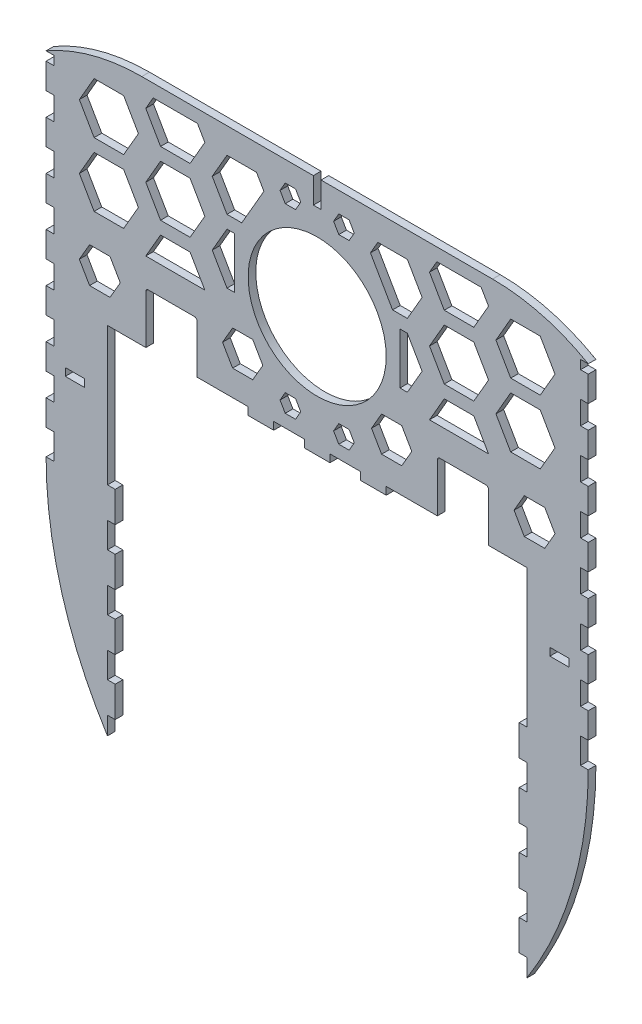
SolidWorks part; units mm, degrees
material "birch 3mm plywood"
ref_plane "Front" through (0, 0, 0) normal (0, 0, 1) x (1, 0, 0)
ref_plane "Top" through (0, 0, 0) normal (0, 1, 0) x (1, 0, 0)
ref_plane "Right" through (0, 0, 0) normal (1, 0, 0) x (0, 0, -1)
sketch "Sketch1" plane through (0, 0, 0) normal (0, 0, 1) x (1, 0, 0)
  line L0 (-106, 24.7134) -> (-106, 14.7134) construction
  line L1 (-82, 17.2134) -> (-82, 27.2134)
  line L2 (-103, 152.2134) -> (-106, 152.2134) construction
  line L3 (-103, 14.7134) -> (-106, 14.7134) construction
  line L4 (-103, 152.2134) -> (-103, 14.7134) construction
  line L5 (-47, 71.2134) -> (-27, 71.2134)
  line L7 (-103, 152.2134) -> (-106, 152.2134)
  line L8 (-103, 14.7134) -> (-106, 14.7134)
  line L9 (-103, 152.2134) -> (-103, 148.7134)
  line L10 (0, 0) -> (0, 68.2134) construction
  line L11 (-82, -67.7866) -> (-82, -60.7866)
  line L12 (-68.5834, 162.2134) -> (68.5834, 162.2134)
  line L13 (-82, 27.2134) -> (-82, 71.2134)
  line L18 (-47, 71.2134) -> (-47, 90.2134)
  line L19 (-48, 91.2134) -> (-66, 91.2134)
  line L20 (-67, 90.2134) -> (-67, 71.2134)
  line L22 (-103, 24.7134) -> (-106, 24.7134)
  line L24 (-103, 34.7134) -> (-106, 34.7134)
  line L25 (-106, 24.7134) -> (-106, 34.7134)
  line L26 (-103, 43.7134) -> (-106, 43.7134)
  line L27 (-106, 43.7134) -> (-106, 53.7134)
  line L28 (-103, 53.7134) -> (-106, 53.7134)
  line L30 (-103, 62.7134) -> (-106, 62.7134)
  line L31 (-106, 62.7134) -> (-106, 72.7134)
  line L32 (-103, 72.7134) -> (-106, 72.7134)
  line L34 (-103, 81.7134) -> (-106, 81.7134)
  line L35 (-106, 81.7134) -> (-106, 91.7134)
  line L36 (-103, 91.7134) -> (-106, 91.7134)
  line L38 (-103, 100.7134) -> (-106, 100.7134)
  line L39 (-106, 100.7134) -> (-106, 110.7134)
  line L40 (-103, 110.7134) -> (-106, 110.7134)
  line L42 (-103, 119.7134) -> (-106, 119.7134)
  line L43 (-106, 119.7134) -> (-106, 129.7134)
  line L44 (-103, 129.7134) -> (-106, 129.7134)
  line L46 (-103, 138.7134) -> (-106, 138.7134)
  line L47 (-106, 138.7134) -> (-106, 148.7134)
  line L48 (-103, 148.7134) -> (-106, 148.7134)
  line L49 (-103, 138.7134) -> (-103, 129.7134)
  line L50 (-103, 119.7134) -> (-103, 110.7134)
  line L51 (-103, 100.7134) -> (-103, 91.7134)
  line L52 (-103, 81.7134) -> (-103, 72.7134)
  line L53 (-103, 62.7134) -> (-103, 53.7134)
  line L54 (-103, 43.7134) -> (-103, 34.7134)
  line L55 (-103, 24.7134) -> (-103, 14.7134)
  line L56 (-82, 71.2134) -> (-67, 71.2134)
  line L57 (-82, 17.2134) -> (-82, 27.2134)
  line L58 (-82, -4.7866) -> (-82, 5.2134)
  line L59 (-82, -26.7866) -> (-82, -16.7866)
  line L60 (-17, 71.2134) -> (-5, 71.2134)
  line L61 (-82, -48.7866) -> (-82, -38.7866)
  line L62 (106, 24.7134) -> (106, 14.7134) construction
  line L63 (79, -16.7866) -> (82, -16.7866)
  line L64 (79, -4.7866) -> (79, -16.7866)
  line L65 (82, -4.7866) -> (79, -4.7866)
  line L66 (82, 5.2134) -> (82, -4.7866)
  line L67 (79, 5.2134) -> (82, 5.2134)
  line L68 (79, 17.2134) -> (79, 5.2134)
  line L69 (82, 17.2134) -> (79, 17.2134)
  line L70 (82, 27.2134) -> (82, 17.2134)
  line L71 (0, 162.2134) -> (0, 68.2134) construction
  line L78 (82, 71.2134) -> (82, 27.2134)
  line L79 (67, 71.2134) -> (82, 71.2134)
  line L80 (-88.6, 48.7134) -> (-93.6, 48.7134)
  line L81 (-82, -16.7866) -> (-82, -26.7866)
  line L82 (-98.6, 45.7134) -> (-98.6, 45.0905)
  line L83 (-82, -26.7866) -> (-79, -26.7866)
  line L84 (-82, 45.7134) -> (-88.6, 45.7134)
  line L85 (-79, -26.7866) -> (-79, -38.7866)
  line L86 (-88.6, 45.7134) -> (-88.6, 48.7134)
  line L87 (-79, -38.7866) -> (-82, -38.7866)
  line L89 (-82, -67.7866) -> (82, -67.7866)
  line L110 (82, 45.7134) -> (82, 49.2134)
  line L111 (82, 49.2134) -> (79, 49.2134)
  line L112 (79, 49.2134) -> (79, 61.2134)
  line L113 (79, 61.2134) -> (82, 61.2134)
  line L114 (82, 61.2134) -> (82, 71.2134)
  line L115 (82, 71.2134) -> (71, 71.2134)
  line L116 (71, 71.2134) -> (71, 68.2134)
  line L117 (71, 68.2134) -> (61, 68.2134)
  line L118 (61, 68.2134) -> (61, 71.2134)
  line L119 (61, 71.2134) -> (49, 71.2134)
  line L120 (49, 71.2134) -> (49, 68.2134)
  line L121 (49, 68.2134) -> (39, 68.2134)
  line L122 (39, 68.2134) -> (39, 71.2134)
  line L123 (39, 71.2134) -> (27, 71.2134)
  line L124 (27, 71.2134) -> (27, 68.2134)
  line L125 (27, 68.2134) -> (17, 68.2134)
  line L126 (17, 68.2134) -> (17, 71.2134)
  line L127 (17, 71.2134) -> (5, 71.2134)
  line L128 (5, 71.2134) -> (5, 68.2134)
  line L129 (5, 68.2134) -> (-5, 68.2134)
  line L130 (-5, 68.2134) -> (-5, 71.2134)
  line L131 (-5, 71.2134) -> (-17, 71.2134)
  line L132 (-17, 71.2134) -> (-17, 68.2134)
  line L133 (-17, 68.2134) -> (-27, 68.2134)
  line L134 (-27, 68.2134) -> (-27, 71.2134)
  line L135 (-27, 71.2134) -> (-39, 71.2134)
  line L136 (-39, 71.2134) -> (-39, 68.2134)
  line L137 (-39, 68.2134) -> (-49, 68.2134)
  line L138 (-49, 68.2134) -> (-49, 71.2134)
  line L139 (-49, 71.2134) -> (-61, 71.2134)
  line L140 (-61, 71.2134) -> (-61, 68.2134)
  line L141 (-61, 68.2134) -> (-71, 68.2134)
  line L142 (-71, 68.2134) -> (-71, 71.2134)
  line L143 (-71, 71.2134) -> (-82, 71.2134)
  line L144 (-82, 71.2134) -> (-82, 61.2134)
  line L145 (-82, 61.2134) -> (-79, 61.2134)
  line L146 (-79, 61.2134) -> (-79, 49.2134)
  line L147 (-79, 49.2134) -> (-82, 49.2134)
  line L148 (-82, 49.2134) -> (-82, 45.7134)
  line L209 (5, 68.2134) -> (-5, 68.2134)
  line L210 (-5, 68.2134) -> (-5, 71.2134)
  line L211 (-5, 71.2134) -> (-17, 71.2134)
  line L212 (-17, 71.2134) -> (-17, 68.2134)
  line L213 (-17, 68.2134) -> (-27, 68.2134)
  line L214 (-27, 68.2134) -> (-27, 71.2134)
  line L215 (-27, 71.2134) -> (-47, 71.2134)
  line L223 (-67, 71.2134) -> (-82, 71.2134)
  line L240 (27, 71.2134) -> (47, 71.2134)
  line L241 (27, 68.2134) -> (27, 71.2134)
  line L242 (17, 68.2134) -> (27, 68.2134)
  line L243 (17, 71.2134) -> (17, 68.2134)
  line L244 (5, 71.2134) -> (17, 71.2134)
  line L245 (5, 68.2134) -> (5, 71.2134)
  line L246 (82, -60.7866) -> (82, -67.7866)
  line L247 (79, -60.7866) -> (82, -60.7866)
  line L248 (79, -48.7866) -> (79, -60.7866)
  line L249 (82, -48.7866) -> (79, -48.7866)
  line L250 (82, -38.7866) -> (82, -48.7866)
  line L251 (79, -38.7866) -> (82, -38.7866)
  line L252 (79, -26.7866) -> (79, -38.7866)
  line L253 (82, -26.7866) -> (79, -26.7866)
  line L254 (82, -16.7866) -> (82, -26.7866)
  line L255 (82, -48.7866) -> (82, -38.7866)
  line L256 (17, 71.2134) -> (5, 71.2134)
  line L257 (82, -26.7866) -> (82, -16.7866)
  line L258 (82, -4.7866) -> (82, 5.2134)
  line L259 (82, 17.2134) -> (82, 27.2134)
  line L260 (82, 71.2134) -> (67, 71.2134)
  line L261 (103, 24.7134) -> (103, 14.7134)
  line L262 (103, 43.7134) -> (103, 34.7134)
  line L263 (103, 62.7134) -> (103, 53.7134)
  line L264 (103, 81.7134) -> (103, 72.7134)
  line L265 (103, 100.7134) -> (103, 91.7134)
  line L266 (103, 119.7134) -> (103, 110.7134)
  line L267 (103, 138.7134) -> (103, 129.7134)
  line L268 (103, 148.7134) -> (106, 148.7134)
  line L269 (106, 138.7134) -> (106, 148.7134)
  line L270 (103, 138.7134) -> (106, 138.7134)
  line L271 (103, 129.7134) -> (106, 129.7134)
  line L272 (106, 119.7134) -> (106, 129.7134)
  line L273 (103, 119.7134) -> (106, 119.7134)
  line L274 (103, 110.7134) -> (106, 110.7134)
  line L275 (106, 100.7134) -> (106, 110.7134)
  line L276 (103, 100.7134) -> (106, 100.7134)
  line L277 (103, 91.7134) -> (106, 91.7134)
  line L278 (106, 81.7134) -> (106, 91.7134)
  line L279 (103, 81.7134) -> (106, 81.7134)
  line L280 (103, 72.7134) -> (106, 72.7134)
  line L281 (106, 62.7134) -> (106, 72.7134)
  line L282 (103, 62.7134) -> (106, 62.7134)
  line L283 (103, 53.7134) -> (106, 53.7134)
  line L284 (106, 43.7134) -> (106, 53.7134)
  line L285 (103, 43.7134) -> (106, 43.7134)
  line L286 (106, 24.7134) -> (106, 34.7134)
  line L287 (103, 34.7134) -> (106, 34.7134)
  line L288 (103, 24.7134) -> (106, 24.7134)
  line L289 (67, 90.2134) -> (67, 71.2134)
  line L290 (48, 91.2134) -> (66, 91.2134)
  line L291 (47, 71.2134) -> (47, 90.2134)
  line L293 (82, -67.7866) -> (82, -60.7866)
  line L294 (103, 152.2134) -> (103, 148.7134)
  line L295 (103, 14.7134) -> (106, 14.7134)
  line L296 (103, 152.2134) -> (106, 152.2134)
  line L297 (-82, -38.7866) -> (-82, -48.7866)
  line L298 (47, 71.2134) -> (27, 71.2134)
  line L299 (0, 162.2134) -> (0, 189.65) construction
  line L300 (-82, -48.7866) -> (-79, -48.7866)
  line L301 (82, 17.2134) -> (82, 27.2134)
  line L404 (-79, -48.7866) -> (-79, -60.7866)
  line L405 (-79, -60.7866) -> (-82, -60.7866)
  line L406 (-82, -60.7866) -> (-82, -67.7866)
  line L407 (-82, 71.2134) -> (-82, 27.2134)
  line L408 (-82, 27.2134) -> (-82, 17.2134)
  line L409 (-82, 17.2134) -> (-79, 17.2134)
  line L410 (-79, 17.2134) -> (-79, 5.2134)
  line L411 (-79, 5.2134) -> (-82, 5.2134)
  line L412 (-82, 5.2134) -> (-82, -4.7866)
  line L413 (-82, -4.7866) -> (-79, -4.7866)
  line L414 (-79, -4.7866) -> (-79, -16.7866)
  line L415 (-79, -16.7866) -> (-82, -16.7866)
  line L456 (-93.6, 48.7134) -> (-93.6, 45.7134)
  line L458 (-93.6, 45.7134) -> (-98.6, 45.7134)
  line L460 (98.6, 45.0905) -> (98.6, 45.7134)
  line L462 (98.6, 45.7134) -> (93.6, 45.7134)
  line L464 (93.6, 45.7134) -> (93.6, 48.7134)
  line L466 (93.6, 48.7134) -> (88.6, 48.7134)
  line L468 (88.6, 48.7134) -> (88.6, 45.7134)
  line L470 (88.6, 45.7134) -> (82, 45.7134)
  arc A0 (-68.5834, 162.2134) -> (-106, 152.2134) centre (-68.5834, 87.2134) ccw
  arc A1 (-106, 14.7134) -> (-82, -67.7866) centre (47.7969, 14.7134) ccw
  arc A4 (-47, 90.2134) -> (-48, 91.2134) centre (-48, 90.2134) ccw
  arc A5 (-66, 91.2134) -> (-67, 90.2134) centre (-66, 90.2134) ccw
  arc A6 (66, 91.2134) -> (67, 90.2134) centre (66, 90.2134) cw
  arc A7 (47, 90.2134) -> (48, 91.2134) centre (48, 90.2134) cw
  arc A8 (106, 14.7134) -> (82, -67.7866) centre (-47.7969, 14.7134) cw
  arc A9 (68.5834, 162.2134) -> (106, 152.2134) centre (68.5834, 87.2134) cw
  circle A10 centre (0, 115.2134) radius 27
  arc A15 (-98.6, 45.0905) -> (-82, -67.7866) centre (293.4723, 45.0905) ccw
  arc A17 (82, -67.7866) -> (98.6, 45.0905) centre (-293.4723, 45.0905) ccw
  dimension "D8" = 75
  dimension "D9" = 20
  dimension "D10" = 15
  dimension "D12" = 1
  dimension "D13" = 1
  dimension "D2" = 10
  dimension "D3" = 20
  dimension "D4" = 10
  dimension "D5" = 10
  dimension "D7" = 9
  dimension "D11" = 20
  dimension "D14" = 3
  dimension "D15" = 3
  dimension "D16" = 12
  dimension "D17" = 10
  dimension "D1" = 0
  dimension "D6" = 7
extrude "Boss-Extrude1" add sketch "Sketch1" along normal blind 3
sketch "Sketch2" plane through (0, 0, 3) normal (0, 0, 1) x (1, 0, 0)
  line L4 (-98.5, 45.7134) -> (-91, 45.7134)
  line L5 (-91, 45.7134) -> (-91, 48.7134)
  line L6 (-91, 48.7134) -> (-98.5, 48.7134)
  line L7 (-98.5, 48.7134) -> (-98.5, 45.7134)
  line L8 (-98.5, 45.7134) -> (-91, 45.7134)
  line L9 (-91, 45.7134) -> (-91, 48.7134)
  line L10 (-91, 48.7134) -> (-98.5, 48.7134)
  line L11 (-98.5, 48.7134) -> (-98.5, 45.7134)
  line L12 (91, 45.7134) -> (98.5, 45.7134)
  line L13 (98.5, 45.7134) -> (98.5, 48.7134)
  line L14 (98.5, 48.7134) -> (91, 48.7134)
  line L15 (91, 48.7134) -> (91, 45.7134)
  line L16 (91, 45.7134) -> (98.5, 45.7134)
  line L17 (98.5, 45.7134) -> (98.5, 48.7134)
  line L18 (98.5, 48.7134) -> (91, 48.7134)
  line L19 (91, 48.7134) -> (91, 45.7134)
  line L20 (-1.5, 162.2134) -> (-1.5, 152.2134)
  line L21 (-1.5, 152.2134) -> (1.5, 152.2134)
  line L22 (1.5, 152.2134) -> (1.5, 162.2134)
  line L23 (1.5, 162.2134) -> (-1.5, 162.2134)
  line L24 (-1.5, 162.2134) -> (-1.5, 152.2134)
  line L25 (-1.5, 152.2134) -> (1.5, 152.2134)
  line L26 (1.5, 152.2134) -> (1.5, 162.2134)
  line L27 (1.5, 162.2134) -> (-1.5, 162.2134)
  line L118 (68.5834, 162.2134) -> (-68.5834, 162.2134)
  line L119 (-106, 152.2134) -> (-103, 152.2134)
  line L120 (-103, 152.2134) -> (-103, 148.7134)
  line L121 (-103, 148.7134) -> (-106, 148.7134)
  line L122 (-106, 148.7134) -> (-106, 138.7134)
  line L123 (-106, 138.7134) -> (-103, 138.7134)
  line L124 (-103, 138.7134) -> (-103, 129.7134)
  line L125 (-103, 129.7134) -> (-106, 129.7134)
  line L126 (-106, 129.7134) -> (-106, 119.7134)
  line L127 (-106, 119.7134) -> (-103, 119.7134)
  line L128 (-103, 119.7134) -> (-103, 110.7134)
  line L129 (-103, 110.7134) -> (-106, 110.7134)
  line L130 (-106, 110.7134) -> (-106, 100.7134)
  line L131 (-106, 100.7134) -> (-103, 100.7134)
  line L132 (-103, 100.7134) -> (-103, 91.7134)
  line L133 (-103, 91.7134) -> (-106, 91.7134)
  line L134 (-106, 91.7134) -> (-106, 81.7134)
  line L135 (-106, 81.7134) -> (-103, 81.7134)
  line L136 (-103, 81.7134) -> (-103, 72.7134)
  line L137 (-103, 72.7134) -> (-106, 72.7134)
  line L138 (-106, 72.7134) -> (-106, 62.7134)
  line L139 (-106, 62.7134) -> (-103, 62.7134)
  line L140 (-103, 62.7134) -> (-103, 53.7134)
  line L141 (-103, 53.7134) -> (-106, 53.7134)
  line L142 (-106, 53.7134) -> (-106, 43.7134)
  line L143 (-106, 43.7134) -> (-103, 43.7134)
  line L144 (-103, 43.7134) -> (-103, 34.7134)
  line L145 (-103, 34.7134) -> (-106, 34.7134)
  line L146 (-106, 34.7134) -> (-106, 24.7134)
  line L147 (-106, 24.7134) -> (-103, 24.7134)
  line L148 (-103, 24.7134) -> (-103, 14.7134)
  line L149 (-103, 14.7134) -> (-106, 14.7134)
  line L150 (-82, -67.7866) -> (-82, -60.7866)
  line L151 (-82, -60.7866) -> (-79, -60.7866)
  line L152 (-79, -60.7866) -> (-79, -48.7866)
  line L153 (-79, -48.7866) -> (-82, -48.7866)
  line L154 (-82, -48.7866) -> (-82, -38.7866)
  line L155 (-82, -38.7866) -> (-79, -38.7866)
  line L156 (-79, -38.7866) -> (-79, -26.7866)
  line L157 (-79, -26.7866) -> (-82, -26.7866)
  line L158 (-82, -26.7866) -> (-82, -16.7866)
  line L159 (-82, -16.7866) -> (-79, -16.7866)
  line L160 (-79, -16.7866) -> (-79, -4.7866)
  line L161 (-79, -4.7866) -> (-82, -4.7866)
  line L162 (-82, -4.7866) -> (-82, 5.2134)
  line L163 (-82, 5.2134) -> (-79, 5.2134)
  line L164 (-79, 5.2134) -> (-79, 17.2134)
  line L165 (-79, 17.2134) -> (-82, 17.2134)
  line L166 (-82, 17.2134) -> (-82, 71.2134)
  line L167 (-82, 71.2134) -> (-67, 71.2134)
  line L168 (-67, 71.2134) -> (-67, 90.2134)
  line L169 (-66, 91.2134) -> (-48, 91.2134)
  line L170 (-47, 90.2134) -> (-47, 71.2134)
  line L171 (-47, 71.2134) -> (-27, 71.2134)
  line L172 (-27, 71.2134) -> (-27, 68.2134)
  line L173 (-27, 68.2134) -> (-17, 68.2134)
  line L174 (-17, 68.2134) -> (-17, 71.2134)
  line L175 (-17, 71.2134) -> (-5, 71.2134)
  line L176 (-5, 71.2134) -> (-5, 68.2134)
  line L177 (-5, 68.2134) -> (5, 68.2134)
  line L178 (5, 68.2134) -> (5, 71.2134)
  line L179 (5, 71.2134) -> (17, 71.2134)
  line L180 (17, 71.2134) -> (17, 68.2134)
  line L181 (17, 68.2134) -> (27, 68.2134)
  line L182 (27, 68.2134) -> (27, 71.2134)
  line L183 (27, 71.2134) -> (47, 71.2134)
  line L184 (47, 71.2134) -> (47, 90.2134)
  line L185 (48, 91.2134) -> (66, 91.2134)
  line L186 (67, 90.2134) -> (67, 71.2134)
  line L187 (67, 71.2134) -> (82, 71.2134)
  line L188 (82, 71.2134) -> (82, 17.2134)
  line L189 (82, 17.2134) -> (79, 17.2134)
  line L190 (79, 17.2134) -> (79, 5.2134)
  line L191 (79, 5.2134) -> (82, 5.2134)
  line L192 (82, 5.2134) -> (82, -4.7866)
  line L193 (82, -4.7866) -> (79, -4.7866)
  line L194 (79, -4.7866) -> (79, -16.7866)
  line L195 (79, -16.7866) -> (82, -16.7866)
  line L196 (82, -16.7866) -> (82, -26.7866)
  line L197 (82, -26.7866) -> (79, -26.7866)
  line L198 (79, -26.7866) -> (79, -38.7866)
  line L199 (79, -38.7866) -> (82, -38.7866)
  line L200 (82, -38.7866) -> (82, -48.7866)
  line L201 (82, -48.7866) -> (79, -48.7866)
  line L202 (79, -48.7866) -> (79, -60.7866)
  line L203 (79, -60.7866) -> (82, -60.7866)
  line L204 (82, -60.7866) -> (82, -67.7866)
  line L205 (106, 14.7134) -> (103, 14.7134)
  line L206 (103, 14.7134) -> (103, 24.7134)
  line L207 (103, 24.7134) -> (106, 24.7134)
  line L208 (106, 24.7134) -> (106, 34.7134)
  line L209 (106, 34.7134) -> (103, 34.7134)
  line L210 (103, 34.7134) -> (103, 43.7134)
  line L211 (103, 43.7134) -> (106, 43.7134)
  line L212 (106, 43.7134) -> (106, 53.7134)
  line L213 (106, 53.7134) -> (103, 53.7134)
  line L214 (103, 53.7134) -> (103, 62.7134)
  line L215 (103, 62.7134) -> (106, 62.7134)
  line L216 (106, 62.7134) -> (106, 72.7134)
  line L217 (106, 72.7134) -> (103, 72.7134)
  line L218 (103, 72.7134) -> (103, 81.7134)
  line L219 (103, 81.7134) -> (106, 81.7134)
  line L220 (106, 81.7134) -> (106, 91.7134)
  line L221 (106, 91.7134) -> (103, 91.7134)
  line L222 (103, 91.7134) -> (103, 100.7134)
  line L223 (103, 100.7134) -> (106, 100.7134)
  line L224 (106, 100.7134) -> (106, 110.7134)
  line L225 (106, 110.7134) -> (103, 110.7134)
  line L226 (103, 110.7134) -> (103, 119.7134)
  line L227 (103, 119.7134) -> (106, 119.7134)
  line L228 (106, 119.7134) -> (106, 129.7134)
  line L229 (106, 129.7134) -> (103, 129.7134)
  line L230 (103, 129.7134) -> (103, 138.7134)
  line L231 (103, 138.7134) -> (106, 138.7134)
  line L232 (106, 138.7134) -> (106, 148.7134)
  line L233 (106, 148.7134) -> (103, 148.7134)
  line L234 (103, 148.7134) -> (103, 152.2134)
  line L235 (103, 152.2134) -> (106, 152.2134)
  line L236 (68.5834, 162.2134) -> (-68.5834, 162.2134)
  line L237 (-106, 152.2134) -> (-103, 152.2134)
  line L238 (-103, 152.2134) -> (-103, 148.7134)
  line L239 (-103, 148.7134) -> (-106, 148.7134)
  line L240 (-106, 148.7134) -> (-106, 138.7134)
  line L241 (-106, 138.7134) -> (-103, 138.7134)
  line L242 (-103, 138.7134) -> (-103, 129.7134)
  line L243 (-103, 129.7134) -> (-106, 129.7134)
  line L244 (-106, 129.7134) -> (-106, 119.7134)
  line L245 (-106, 119.7134) -> (-103, 119.7134)
  line L246 (-103, 119.7134) -> (-103, 110.7134)
  line L247 (-103, 110.7134) -> (-106, 110.7134)
  line L248 (-106, 110.7134) -> (-106, 100.7134)
  line L249 (-106, 100.7134) -> (-103, 100.7134)
  line L250 (-103, 100.7134) -> (-103, 91.7134)
  line L251 (-103, 91.7134) -> (-106, 91.7134)
  line L252 (-106, 91.7134) -> (-106, 81.7134)
  line L253 (-106, 81.7134) -> (-103, 81.7134)
  line L254 (-103, 81.7134) -> (-103, 72.7134)
  line L255 (-103, 72.7134) -> (-106, 72.7134)
  line L256 (-106, 72.7134) -> (-106, 62.7134)
  line L257 (-106, 62.7134) -> (-103, 62.7134)
  line L258 (-103, 62.7134) -> (-103, 53.7134)
  line L259 (-103, 53.7134) -> (-106, 53.7134)
  line L260 (-106, 53.7134) -> (-106, 43.7134)
  line L261 (-106, 43.7134) -> (-103, 43.7134)
  line L262 (-103, 43.7134) -> (-103, 34.7134)
  line L263 (-103, 34.7134) -> (-106, 34.7134)
  line L264 (-106, 34.7134) -> (-106, 24.7134)
  line L265 (-106, 24.7134) -> (-103, 24.7134)
  line L266 (-103, 24.7134) -> (-103, 14.7134)
  line L267 (-103, 14.7134) -> (-106, 14.7134)
  line L268 (-82, -67.7866) -> (-82, -60.7866)
  line L269 (-82, -60.7866) -> (-79, -60.7866)
  line L270 (-79, -60.7866) -> (-79, -48.7866)
  line L271 (-79, -48.7866) -> (-82, -48.7866)
  line L272 (-82, -48.7866) -> (-82, -38.7866)
  line L273 (-82, -38.7866) -> (-79, -38.7866)
  line L274 (-79, -38.7866) -> (-79, -26.7866)
  line L275 (-79, -26.7866) -> (-82, -26.7866)
  line L276 (-82, -26.7866) -> (-82, -16.7866)
  line L277 (-82, -16.7866) -> (-79, -16.7866)
  line L278 (-79, -16.7866) -> (-79, -4.7866)
  line L279 (-79, -4.7866) -> (-82, -4.7866)
  line L280 (-82, -4.7866) -> (-82, 5.2134)
  line L281 (-82, 5.2134) -> (-79, 5.2134)
  line L282 (-79, 5.2134) -> (-79, 17.2134)
  line L283 (-79, 17.2134) -> (-82, 17.2134)
  line L284 (-82, 17.2134) -> (-82, 71.2134)
  line L285 (-82, 71.2134) -> (-67, 71.2134)
  line L286 (-67, 71.2134) -> (-67, 90.2134)
  line L287 (-66, 91.2134) -> (-48, 91.2134)
  line L288 (-47, 90.2134) -> (-47, 71.2134)
  line L289 (-47, 71.2134) -> (-27, 71.2134)
  line L290 (-27, 71.2134) -> (-27, 68.2134)
  line L291 (-27, 68.2134) -> (-17, 68.2134)
  line L292 (-17, 68.2134) -> (-17, 71.2134)
  line L293 (-17, 71.2134) -> (-5, 71.2134)
  line L294 (-5, 71.2134) -> (-5, 68.2134)
  line L295 (-5, 68.2134) -> (5, 68.2134)
  line L296 (5, 68.2134) -> (5, 71.2134)
  line L297 (5, 71.2134) -> (17, 71.2134)
  line L298 (17, 71.2134) -> (17, 68.2134)
  line L299 (17, 68.2134) -> (27, 68.2134)
  line L300 (27, 68.2134) -> (27, 71.2134)
  line L301 (27, 71.2134) -> (47, 71.2134)
  line L302 (47, 71.2134) -> (47, 90.2134)
  line L303 (48, 91.2134) -> (66, 91.2134)
  line L304 (67, 90.2134) -> (67, 71.2134)
  line L305 (67, 71.2134) -> (82, 71.2134)
  line L306 (82, 71.2134) -> (82, 17.2134)
  line L307 (82, 17.2134) -> (79, 17.2134)
  line L308 (79, 17.2134) -> (79, 5.2134)
  line L309 (79, 5.2134) -> (82, 5.2134)
  line L310 (82, 5.2134) -> (82, -4.7866)
  line L311 (82, -4.7866) -> (79, -4.7866)
  line L312 (79, -4.7866) -> (79, -16.7866)
  line L313 (79, -16.7866) -> (82, -16.7866)
  line L314 (82, -16.7866) -> (82, -26.7866)
  line L315 (82, -26.7866) -> (79, -26.7866)
  line L316 (79, -26.7866) -> (79, -38.7866)
  line L317 (79, -38.7866) -> (82, -38.7866)
  line L318 (82, -38.7866) -> (82, -48.7866)
  line L319 (82, -48.7866) -> (79, -48.7866)
  line L320 (79, -48.7866) -> (79, -60.7866)
  line L321 (79, -60.7866) -> (82, -60.7866)
  line L322 (82, -60.7866) -> (82, -67.7866)
  line L323 (106, 14.7134) -> (103, 14.7134)
  line L324 (103, 14.7134) -> (103, 24.7134)
  line L325 (103, 24.7134) -> (106, 24.7134)
  line L326 (106, 24.7134) -> (106, 34.7134)
  line L327 (106, 34.7134) -> (103, 34.7134)
  line L328 (103, 34.7134) -> (103, 43.7134)
  line L329 (103, 43.7134) -> (106, 43.7134)
  line L330 (106, 43.7134) -> (106, 53.7134)
  line L331 (106, 53.7134) -> (103, 53.7134)
  line L332 (103, 53.7134) -> (103, 62.7134)
  line L333 (103, 62.7134) -> (106, 62.7134)
  line L334 (106, 62.7134) -> (106, 72.7134)
  line L335 (106, 72.7134) -> (103, 72.7134)
  line L336 (103, 72.7134) -> (103, 81.7134)
  line L337 (103, 81.7134) -> (106, 81.7134)
  line L338 (106, 81.7134) -> (106, 91.7134)
  line L339 (106, 91.7134) -> (103, 91.7134)
  line L340 (103, 91.7134) -> (103, 100.7134)
  line L341 (103, 100.7134) -> (106, 100.7134)
  line L342 (106, 100.7134) -> (106, 110.7134)
  line L343 (106, 110.7134) -> (103, 110.7134)
  line L344 (103, 110.7134) -> (103, 119.7134)
  line L345 (103, 119.7134) -> (106, 119.7134)
  line L346 (106, 119.7134) -> (106, 129.7134)
  line L347 (106, 129.7134) -> (103, 129.7134)
  line L348 (103, 129.7134) -> (103, 138.7134)
  line L349 (103, 138.7134) -> (106, 138.7134)
  line L350 (106, 138.7134) -> (106, 148.7134)
  line L351 (106, 148.7134) -> (103, 148.7134)
  line L352 (103, 148.7134) -> (103, 152.2134)
  line L353 (103, 152.2134) -> (106, 152.2134)
  arc A8 (106, 152.2134) -> (68.5834, 162.2134) centre (68.5834, 87.2134) ccw
  arc A9 (-68.5834, 162.2134) -> (-106, 152.2134) centre (-68.5834, 87.2134) ccw
  arc A10 (-106, 14.7134) -> (-82, -67.7866) centre (47.7969, 14.7134) ccw
  arc A11 (-66, 91.2134) -> (-67, 90.2134) centre (-66, 90.2134) ccw
  arc A12 (-47, 90.2134) -> (-48, 91.2134) centre (-48, 90.2134) ccw
  arc A13 (48, 91.2134) -> (47, 90.2134) centre (48, 90.2134) ccw
  arc A14 (67, 90.2134) -> (66, 91.2134) centre (66, 90.2134) ccw
  arc A15 (82, -67.7866) -> (106, 14.7134) centre (-47.7969, 14.7134) ccw
  arc A16 (106, 152.2134) -> (68.5834, 162.2134) centre (68.5834, 87.2134) ccw
  arc A17 (-68.5834, 162.2134) -> (-106, 152.2134) centre (-68.5834, 87.2134) ccw
  arc A18 (-106, 14.7134) -> (-82, -67.7866) centre (47.7969, 14.7134) ccw
  arc A19 (-66, 91.2134) -> (-67, 90.2134) centre (-66, 90.2134) ccw
  arc A20 (-47, 90.2134) -> (-48, 91.2134) centre (-48, 90.2134) ccw
  arc A21 (48, 91.2134) -> (47, 90.2134) centre (48, 90.2134) ccw
  arc A22 (67, 90.2134) -> (66, 91.2134) centre (66, 90.2134) ccw
  arc A23 (82, -67.7866) -> (106, 14.7134) centre (-47.7969, 14.7134) ccw
  dimension "D1" = 0
  dimension "D2" = 0
  dimension "D3" = 0
  dimension "D4" = 0
extrude "Cut-Extrude1" cut sketch "Sketch2" against normal blind 3 contours L10 L11 L8 L9 | L24 L25 L26 L27 | L18 L19 L16 L17
sketch "Sketch3" plane through (0, 0, 3) normal (0, 0, 1) x (1, 0, 0)
  line L0 (0, 152.2134) -> (0, 68.2134) construction
  line L1 (-82, 71.2134) -> (-67, 71.2134) construction
  line L2 (-57, 91.2134) -> (-57, 76.3727) construction
  line L3 (0, 115.2134) -> (27, 115.2134) construction
  line L4 (-68.5834, 162.2134) -> (-1.5, 162.2134) construction
  line L5 (-69.906, 142.2134) -> (-75.6795, 152.2134)
  line L6 (-75.6795, 152.2134) -> (-87.2265, 152.2134)
  line L7 (-87.2265, 152.2134) -> (-93, 142.2134)
  line L8 (-93, 142.2134) -> (-87.2265, 132.2134)
  line L9 (-87.2265, 132.2134) -> (-75.6795, 132.2134)
  line L10 (-75.6795, 132.2134) -> (-69.906, 142.2134)
  line L11 (-103, 138.7134) -> (-103, 129.7134) construction
  line L12 (-55.4722, 127.2134) -> (-81.453, 142.2134) construction
  line L13 (-43.9252, 127.2134) -> (-49.6987, 137.2134)
  line L14 (-49.6987, 137.2134) -> (-61.2457, 137.2134)
  line L15 (-61.2457, 137.2134) -> (-67.0192, 127.2134)
  line L16 (-67.0192, 127.2134) -> (-61.2457, 117.2134)
  line L17 (-61.2457, 117.2134) -> (-49.6987, 117.2134)
  line L18 (-49.6987, 117.2134) -> (-43.9252, 127.2134)
  line L19 (-55.4722, 127.2134) -> (-55.4722, 137.2134) construction
  line L20 (-55.4722, 127.2134) -> (-29.4915, 142.2134) construction
  line L21 (-20.8312, 147.2134) -> (-23.718, 152.2134)
  line L22 (-23.718, 152.2134) -> (-35.265, 152.2134)
  line L23 (-35.265, 152.2134) -> (-41.0385, 142.2134)
  line L24 (-41.0385, 142.2134) -> (-35.265, 132.2134)
  line L25 (-35.265, 132.2134) -> (-29.4915, 132.2134)
  line L27 (-43.9252, 152.2134) -> (-46.812, 157.2134)
  line L29 (-64.1325, 157.2134) -> (-67.0192, 152.2134)
  line L30 (-67.0192, 152.2134) -> (-61.2457, 142.2134)
  line L31 (-61.2457, 142.2134) -> (-49.6987, 142.2134)
  line L32 (-49.6987, 142.2134) -> (-43.9252, 152.2134)
  line L33 (-55.4722, 152.2134) -> (-55.4722, 157.2134) construction
  line L34 (-64.1325, 157.2134) -> (-46.812, 157.2134)
  line L36 (-55.4722, 162.2134) -> (-61.2457, 162.2134) [skipped]
  line L37 (-43.9252, 102.2134) -> (-49.6987, 112.2134)
  line L38 (-49.6987, 112.2134) -> (-61.2457, 112.2134)
  line L39 (-61.2457, 112.2134) -> (-67.0192, 102.2134)
  line L42 (-35.265, 107.2134) -> (-32.3782, 107.2134)
  line L45 (-32.3782, 127.2134) -> (-35.265, 127.2134)
  line L46 (-35.265, 127.2134) -> (-41.0385, 117.2134)
  line L47 (-41.0385, 117.2134) -> (-35.265, 107.2134)
  line L48 (-87.2265, 107.2134) -> (-75.6795, 107.2134)
  line L49 (-75.6795, 107.2134) -> (-69.906, 117.2134)
  line L50 (-69.906, 117.2134) -> (-75.6795, 127.2134)
  line L51 (-75.6795, 127.2134) -> (-87.2265, 127.2134)
  line L52 (-87.2265, 127.2134) -> (-93, 117.2134)
  line L53 (-93, 117.2134) -> (-87.2265, 107.2134)
  line L56 (-20.8312, 147.2134) -> (-29.4915, 132.2134)
  line L57 (-47, 71.2134) -> (-47, 90.2134) construction
  line L58 (-23.718, 132.2134) -> (-17.9445, 142.2134) [skipped]
  line L59 (-17.9445, 117.2134) -> (-23.718, 127.2134) [skipped]
  line L60 (-55.4722, 92.2134) -> (-49.6987, 92.2134) [skipped]
  line L61 (-77, 88.1416) -> (-81, 95.0698)
  line L62 (-81, 95.0698) -> (-89, 95.0698)
  line L63 (-89, 95.0698) -> (-93, 88.1416)
  line L64 (-93, 88.1416) -> (-89, 81.2134)
  line L65 (-89, 81.2134) -> (-81, 81.2134)
  line L66 (-81, 81.2134) -> (-77, 88.1416)
  line L67 (-67, 90.2134) -> (-67, 71.2134) construction
  line L68 (-103, 100.7134) -> (-103, 91.7134) construction
  line L75 (-21.2564, 88.0306) -> (-25.1923, 94.8478)
  line L76 (-25.1923, 94.8478) -> (-33.0641, 94.8478)
  line L77 (-33.0641, 94.8478) -> (-37, 88.0306)
  line L78 (-37, 88.0306) -> (-33.0641, 81.2134)
  line L79 (-33.0641, 81.2134) -> (-25.1923, 81.2134)
  line L80 (-25.1923, 81.2134) -> (-21.2564, 88.0306)
  line L81 (-47, 71.2134) -> (-27, 71.2134) construction
  line L82 (-17, 71.2134) -> (-5, 71.2134) construction
  line L83 (-6.4284, 79.7134) -> (-8.4491, 83.2134)
  line L84 (-8.4491, 83.2134) -> (-12.4906, 83.2134)
  line L85 (-12.4906, 83.2134) -> (-14.5113, 79.7134)
  line L86 (-14.5113, 79.7134) -> (-12.4906, 76.2134)
  line L87 (-12.4906, 76.2134) -> (-8.4491, 76.2134)
  line L88 (-8.4491, 76.2134) -> (-6.4284, 79.7134)
  line L89 (-8.4491, 154.2134) -> (-6.4284, 150.7134)
  line L90 (-12.4906, 154.2134) -> (-8.4491, 154.2134)
  line L91 (-14.5113, 150.7134) -> (-12.4906, 154.2134)
  line L92 (-12.4906, 147.2134) -> (-14.5113, 150.7134)
  line L93 (-8.4491, 147.2134) -> (-12.4906, 147.2134)
  line L94 (-6.4284, 150.7134) -> (-8.4491, 147.2134)
  line L95 (55.4722, 152.2134) -> (55.4722, 157.2134) construction
  line L96 (55.4722, 127.2134) -> (29.4915, 142.2134) construction
  line L97 (55.4722, 127.2134) -> (55.4722, 137.2134) construction
  line L98 (55.4722, 127.2134) -> (81.453, 142.2134) construction
  line L99 (0, 115.2134) -> (-27, 115.2134) construction
  line L100 (57, 91.2134) -> (57, 76.3727) construction
  line L101 (6.4284, 150.7134) -> (8.4491, 147.2134)
  line L102 (8.4491, 147.2134) -> (12.4906, 147.2134)
  line L103 (12.4906, 147.2134) -> (14.5113, 150.7134)
  line L104 (14.5113, 150.7134) -> (12.4906, 154.2134)
  line L105 (12.4906, 154.2134) -> (8.4491, 154.2134)
  line L106 (8.4491, 154.2134) -> (6.4284, 150.7134)
  line L107 (8.4491, 76.2134) -> (6.4284, 79.7134)
  line L108 (12.4906, 76.2134) -> (8.4491, 76.2134)
  line L109 (14.5113, 79.7134) -> (12.4906, 76.2134)
  line L110 (12.4906, 83.2134) -> (14.5113, 79.7134)
  line L111 (8.4491, 83.2134) -> (12.4906, 83.2134)
  line L112 (6.4284, 79.7134) -> (8.4491, 83.2134)
  line L113 (25.1923, 81.2134) -> (21.2564, 88.0306)
  line L114 (33.0641, 81.2134) -> (25.1923, 81.2134)
  line L115 (37, 88.0306) -> (33.0641, 81.2134)
  line L116 (33.0641, 94.8478) -> (37, 88.0306)
  line L117 (25.1923, 94.8478) -> (33.0641, 94.8478)
  line L118 (21.2564, 88.0306) -> (25.1923, 94.8478)
  line L119 (81, 81.2134) -> (77, 88.1416)
  line L120 (89, 81.2134) -> (81, 81.2134)
  line L121 (93, 88.1416) -> (89, 81.2134)
  line L122 (89, 95.0698) -> (93, 88.1416)
  line L123 (81, 95.0698) -> (89, 95.0698)
  line L124 (77, 88.1416) -> (81, 95.0698)
  line L125 (20.8312, 147.2134) -> (29.4915, 132.2134)
  line L128 (93, 117.2134) -> (87.2265, 107.2134)
  line L129 (87.2265, 127.2134) -> (93, 117.2134)
  line L130 (75.6795, 127.2134) -> (87.2265, 127.2134)
  line L131 (69.906, 117.2134) -> (75.6795, 127.2134)
  line L132 (75.6795, 107.2134) -> (69.906, 117.2134)
  line L133 (87.2265, 107.2134) -> (75.6795, 107.2134)
  line L134 (41.0385, 117.2134) -> (35.265, 107.2134)
  line L135 (35.265, 127.2134) -> (41.0385, 117.2134)
  line L136 (32.3782, 127.2134) -> (35.265, 127.2134)
  line L137 (35.265, 107.2134) -> (32.3782, 107.2134)
  line L139 (61.2457, 112.2134) -> (67.0192, 102.2134)
  line L140 (49.6987, 112.2134) -> (61.2457, 112.2134)
  line L141 (43.9252, 102.2134) -> (49.6987, 112.2134)
  line L143 (64.1325, 157.2134) -> (46.812, 157.2134)
  line L144 (49.6987, 142.2134) -> (43.9252, 152.2134)
  line L145 (61.2457, 142.2134) -> (49.6987, 142.2134)
  line L146 (67.0192, 152.2134) -> (61.2457, 142.2134)
  line L147 (64.1325, 157.2134) -> (67.0192, 152.2134)
  line L148 (43.9252, 152.2134) -> (46.812, 157.2134)
  line L149 (35.265, 132.2134) -> (29.4915, 132.2134)
  line L150 (41.0385, 142.2134) -> (35.265, 132.2134)
  line L151 (35.265, 152.2134) -> (41.0385, 142.2134)
  line L152 (23.718, 152.2134) -> (35.265, 152.2134)
  line L153 (20.8312, 147.2134) -> (23.718, 152.2134)
  line L154 (49.6987, 117.2134) -> (43.9252, 127.2134)
  line L155 (61.2457, 117.2134) -> (49.6987, 117.2134)
  line L156 (67.0192, 127.2134) -> (61.2457, 117.2134)
  line L157 (61.2457, 137.2134) -> (67.0192, 127.2134)
  line L158 (49.6987, 137.2134) -> (61.2457, 137.2134)
  line L159 (43.9252, 127.2134) -> (49.6987, 137.2134)
  line L160 (75.6795, 132.2134) -> (69.906, 142.2134)
  line L161 (87.2265, 132.2134) -> (75.6795, 132.2134)
  line L162 (93, 142.2134) -> (87.2265, 132.2134)
  line L163 (87.2265, 152.2134) -> (93, 142.2134)
  line L164 (75.6795, 152.2134) -> (87.2265, 152.2134)
  line L165 (69.906, 142.2134) -> (75.6795, 152.2134)
  line L169 (-67.0192, 102.2134) -> (-43.9252, 102.2134)
  line L170 (43.9252, 102.2134) -> (67.0192, 102.2134)
  line L171 (-67.0192, 102.2134) -> (-65.5759, 99.7134) [skipped]
  line L172 (-45.3686, 99.7134) -> (-43.9252, 102.2134) [skipped]
  line L173 (-32.3782, 127.2134) -> (-32.3782, 107.2134)
  line L174 (32.3782, 127.2134) -> (32.3782, 107.2134)
  circle A0 centre (-29.1282, 88.0306) radius 6.8172 construction
  circle A1 centre (-81.453, 142.2134) radius 10 construction
  circle A2 centre (-55.4722, 127.2134) radius 10 construction
  arc A3 (-20.8312, 147.2134) -> (-29.4915, 132.2134) centre (-29.4915, 142.2134) ccw construction
  arc A4 (-64.1325, 157.2134) -> (-46.812, 157.2134) centre (-55.4722, 152.2134) ccw construction
  arc A5 (-45.4722, 102.2134) -> (-65.4722, 102.2134) centre (-55.4722, 102.2134) ccw construction
  arc A6 (-32.3782, 126.7877) -> (-32.3782, 107.6392) centre (-29.4915, 117.2134) ccw construction
  circle A7 centre (-81.453, 117.2134) radius 10 construction
  circle A8 centre (0, 115.2134) radius 27 construction
  circle A9 centre (-85, 88.1416) radius 6.9282 construction
  circle A10 centre (-10.4699, 79.7134) radius 3.5 construction
  circle A11 centre (-10.4699, 150.7134) radius 3.5 construction
  circle A12 centre (10.4699, 150.7134) radius 3.5 construction
  circle A13 centre (10.4699, 79.7134) radius 3.5 construction
  circle A14 centre (85, 88.1416) radius 6.9282 construction
  circle A15 centre (81.453, 117.2134) radius 10 construction
  arc A16 (32.3782, 126.7877) -> (32.3782, 107.6392) centre (29.4915, 117.2134) cw construction
  arc A17 (45.4722, 102.2134) -> (65.4722, 102.2134) centre (55.4722, 102.2134) cw construction
  arc A18 (64.1325, 157.2134) -> (46.812, 157.2134) centre (55.4722, 152.2134) cw construction
  arc A19 (20.8312, 147.2134) -> (29.4915, 132.2134) centre (29.4915, 142.2134) cw construction
  circle A20 centre (55.4722, 127.2134) radius 10 construction
  circle A21 centre (81.453, 142.2134) radius 10 construction
  circle A22 centre (29.1282, 88.0306) radius 6.8172 construction
  dimension "D1" = 20
  dimension "D4" = 2
  dimension "D9" = 5
  dimension "D16" = 32
  dimension "D17" = 32
  dimension "D2" = 10
  dimension "D3" = 10
  dimension "D5" = 10
  dimension "D6" = 60
  dimension "D7" = 60
  dimension "D8" = 10
  dimension "D11" = 10
  dimension "D12" = 10
  dimension "D13" = 10
  dimension "D14" = 10
  dimension "D15" = 10
  dimension "D18" = 5
  dimension "D19" = 10
  dimension "D10" = 2
extrude "Cut-Extrude2" cut sketch "Sketch3" against normal through all
